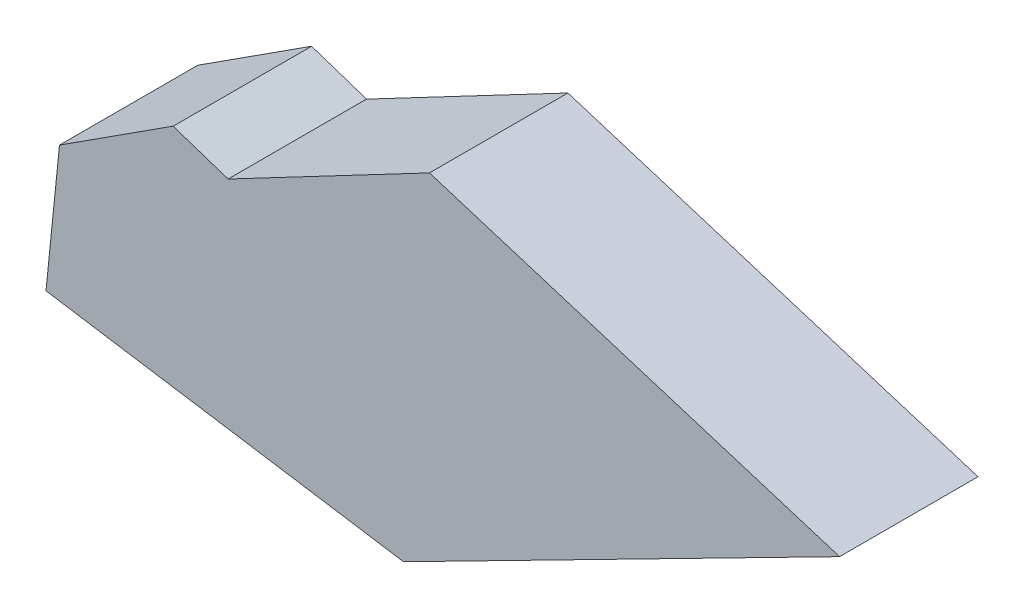
SolidWorks part; units mm, degrees
ref_plane "Front Plane" through (0, 0, 0) normal (0, 0, 1) x (1, 0, 0)
ref_plane "Top Plane" through (0, 0, 0) normal (0, 1, 0) x (1, 0, 0)
ref_plane "Right Plane" through (0, 0, 0) normal (1, 0, 0) x (0, 0, -1)
sketch "Sketch1" plane through (0, 0, 0) normal (0, 0, 1) x (1, 0, 0)
  line L0 (-41.2108, 11.4165) -> (16.9855, 42.0462)
  line L1 (16.9855, 42.0462) -> (135.5108, 5.2625)
  line L2 (135.5108, 5.2625) -> (9.4674, -59.0317)
  line L3 (9.4674, -59.0317) -> (-93.8382, -42.8815)
  line L4 (-93.8382, -42.8815) -> (-89.9398, -4.4552)
  line L5 (-89.9398, -4.4552) -> (-57.0826, 16.7071)
  line L6 (-57.0826, 16.7071) -> (-41.2108, 11.4165)
extrude "Boss-Extrude1" add sketch "Sketch1" along normal blind 40
